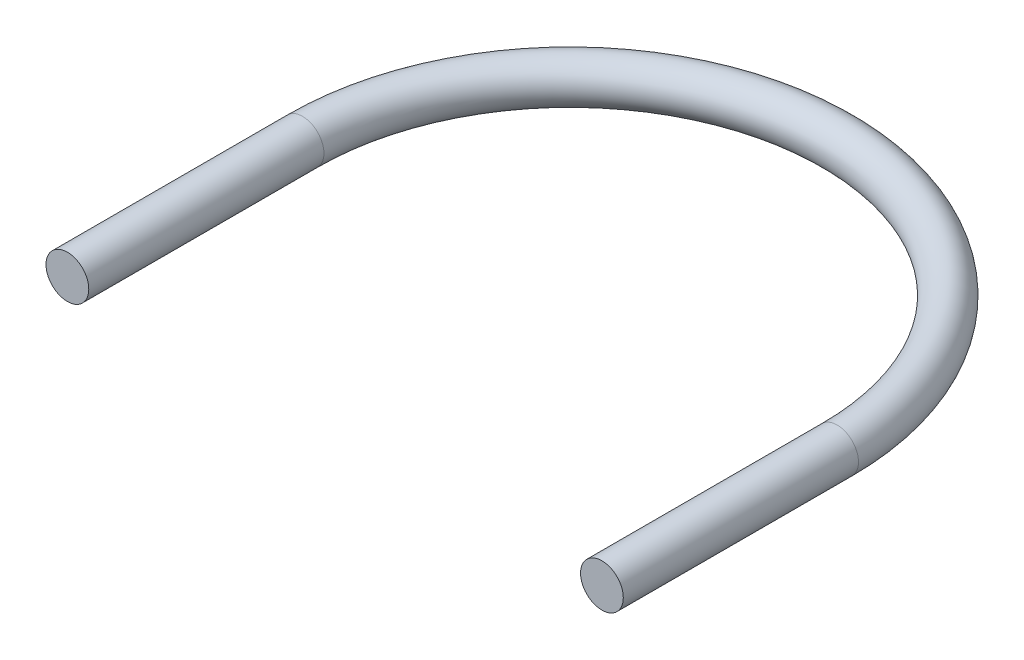
SolidWorks part; units mm, degrees
ref_plane "Front Plane" through (0, 0, 0) normal (0, 0, 1) x (1, 0, 0)
ref_plane "Top Plane" through (0, 0, 0) normal (0, 1, 0) x (1, 0, 0)
ref_plane "Right Plane" through (0, 0, 0) normal (1, 0, 0) x (0, 0, -1)
sketch "Sketch1" plane through (0, 0, 0) normal (1, 0, 0) x (0, 0, -1)
  line L0 (0, 0) -> (-31.75, 0)
  line L1 (-31.75, -9.0598) -> (-31.75, 9.0598)
  circle A0 centre (0, 0) radius 2.54
  point P6 (-31.75, 0)
  dimension "D1" = 5.08
revolve "Revolve1" add sketch "Sketch1" angle 90 about L1
sketch "Sketch2" plane through (0, 0, 31.75) normal (0, 0, 1) x (1, 0, 0)
  circle A0 centre (-31.75, 0) radius 2.54
  circle A1 centre (31.75, 0) radius 2.54
extrude "Boss-Extrude1" add sketch "Sketch2" along normal blind 27.94
